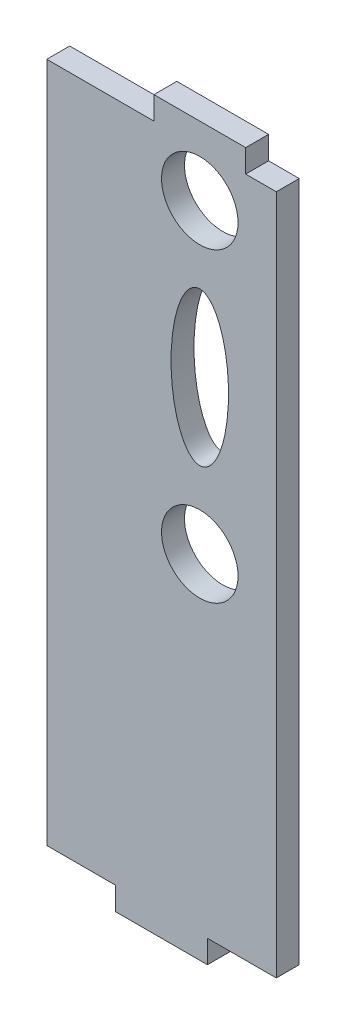
SolidWorks part; units mm, degrees
ref_plane "前视基准面" through (0, 0, 0) normal (0, 0, 1) x (1, 0, 0)
ref_plane "上视基准面" through (0, 0, 0) normal (0, 1, 0) x (1, 0, 0)
ref_plane "右视基准面" through (0, 0, 0) normal (1, 0, 0) x (0, 0, -1)
sketch "草图1" plane through (0, 0, 0) normal (0, 0, 1) x (1, 0, 0)
  line L0 (555.1665, 395.6883) -> (555.1665, 306.6883)
  line L1 (585.1665, 395.6883) -> (585.1665, 306.6883)
  line L2 (555.1665, 306.6883) -> (564.1665, 306.6883)
  line L3 (576.1665, 306.6883) -> (585.1665, 306.6883)
  line L4 (564.1665, 303.6883) -> (576.1665, 303.6883)
  line L5 (555.1665, 395.6883) -> (569.1665, 395.6883)
  line L6 (581.1665, 395.6883) -> (585.1665, 395.6883)
  line L8 (569.1665, 398.6883) -> (581.1665, 398.6883)
  line L9 (564.1665, 303.6883) -> (564.1665, 306.6883)
  line L10 (569.1665, 395.6883) -> (569.1665, 398.6883)
  line L11 (576.1665, 303.6883) -> (576.1665, 306.6883)
  line L12 (581.1665, 395.6883) -> (581.1665, 398.6883)
  circle A0 centre (575.1665, 389.6883) radius 5
  circle A1 centre (575.1665, 349.6883) radius 5
  ellipse E0 centre (575.1665, 369.6883) end of major axis (575.1665, 379.6883) minor radius 3.7571
  dimension "D4" = 6
  dimension "D5" = 40
  dimension "D8" = 10
  dimension "D9" = 10
  dimension "D11" = 9
  dimension "D12" = 10
  dimension "D1" = 89
  dimension "D2" = 30
  dimension "D3" = 89
  dimension "D6" = 20
  dimension "D7" = 20
  dimension "D10" = 6
extrude "凸台-拉伸1" add sketch "草图1" along normal blind 3
